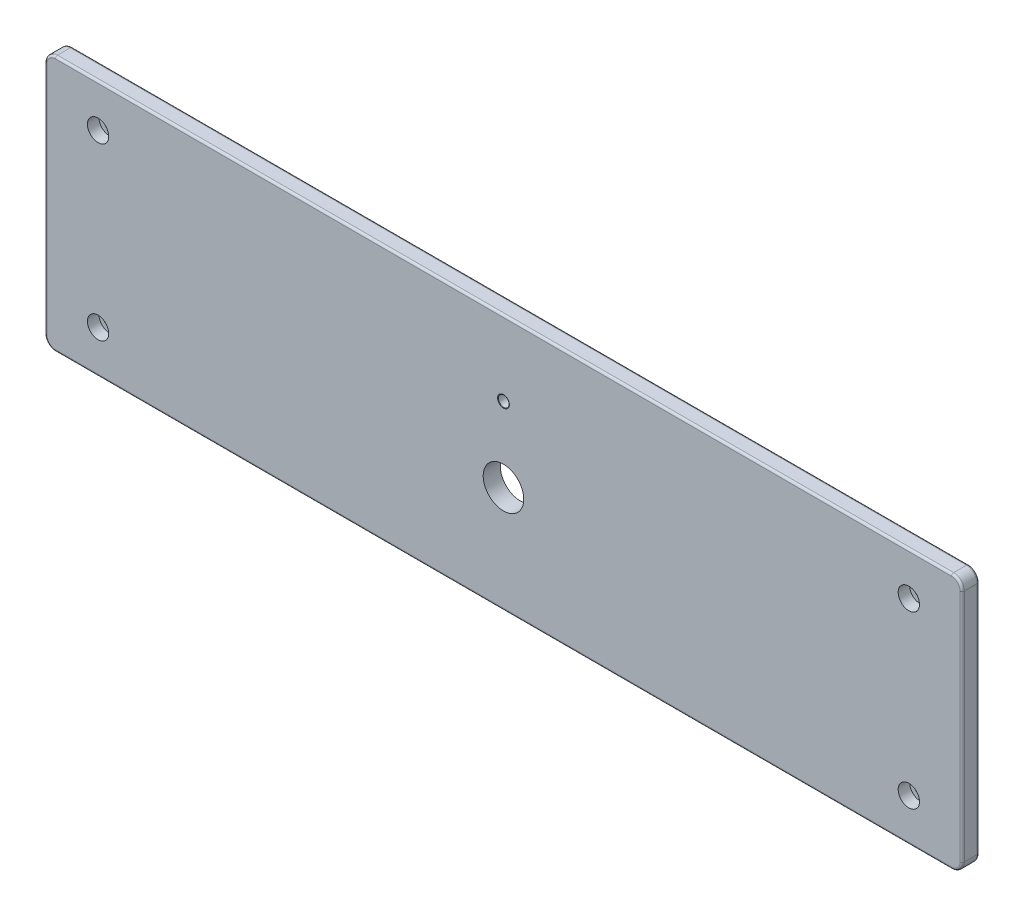
SolidWorks part; units mm, degrees
material "7079 Alloy"
ref_plane "Front Plane" through (0, 0, 0) normal (0, 0, 1) x (1, 0, 0)
ref_plane "Top Plane" through (0, 0, 0) normal (0, 1, 0) x (1, 0, 0)
ref_plane "Right Plane" through (0, 0, 0) normal (1, 0, 0) x (0, 0, -1)
sketch "Sketch1" plane through (0, 0, 0) normal (0, 0, 1) x (1, 0, 0)
  line L1 (0, 0) -> (430, 0)
  line L2 (0, 0) -> (0, 120)
  line L3 (0, 120) -> (430, 120)
  line L4 (430, 0) -> (430, 120)
extrude "Extrude1" add sketch "Sketch1" along normal blind 8
fillet "Fillet1" radius 5 4 edges at (0, 0, 4) (430, 0, 4) (430, 120, 4) (0, 120, 4)
fillet "Fillet2" radius 1 16 edges at (428.5355, 1.4645, 0) (1.4645, 118.5355, 0) (0, 60, 0) (1.4645, 1.4645, 0) (215, 0, 0) (428.5355, 118.5355, 0) (430, 60, 0) (1.4645, 118.5355, 8) (428.5355, 118.5355, 8) (430, 60, 8) (428.5355, 1.4645, 8) (215, 0, 8) (1.4645, 1.4645, 8) (0, 60, 8) (215, 120, 0) (215, 120, 8)
sketch "Sketch2" plane through (0, 0, 8) normal (0, 0, 1) x (1, 0, 0)
  line L0 (25, 20) -> (25, 100) construction
  line L1 (25, 100) -> (405, 100) construction
  line L2 (405, 100) -> (405, 20) construction
  line L3 (405, 20) -> (25, 20) construction
  line L4 (215, 20) -> (215, 50) construction
  line L5 (215, 50) -> (215, 85) construction
  line L6 (215, 85) -> (215, 100) construction
hole_wizard "Ø5.0 (5) Diameter Hole1" positions "3DSketch2" profile "Sketch5" hole size "Ø5.0" standard "DIN" end condition through all
sketch3d "3DSketch2"
  point P0 (215, 85, 8)
sketch "Sketch5" plane through (215, 85, 8) normal (1, 0, 0) x (0, -1, 0)
  line L0 (0, 0) -> (0, 8)
  line L1 (0, 8) -> (2.5, 8)
  line L2 (2.5, 8) -> (2.5, 0)
  line L5 (2.5, 0) -> (0, 0)
  line L11 (0, -6.35) -> (0, 107.95) construction
  dimension "Thru Hole Dia." = 5
  dimension "Thru Hole Depth" = 8
hole_wizard "Ø19.0 (19) Diameter Hole1" positions "3DSketch3" profile "Sketch6" hole size "Ø19.0" standard "DIN" end condition through all
sketch3d "3DSketch3"
  point P0 (215, 50, 8)
sketch "Sketch6" plane through (215, 50, 8) normal (1, 0, 0) x (0, -1, 0)
  line L0 (0, 0) -> (0, 8)
  line L1 (0, 8) -> (9.5, 8)
  line L2 (9.5, 8) -> (9.5, 0)
  line L5 (9.5, 0) -> (0, 0)
  line L11 (0, -6.35) -> (0, 107.95) construction
  dimension "Thru Hole Dia." = 19
  dimension "Thru Hole Depth" = 8
chamfer "Chamfer1" distance 0.25 angle 30 1 edges at (217.5, 85, 8)
hole_wizard "CBORE for M5 Hex Socket Head Cap Screw1" positions "3DSketch4" profile "Sketch9" counterbore size "M5" standard "DIN" end condition through all
sketch3d "3DSketch4"
  point P0 (25, 20, 8)
  point P3 (25, 100, 8)
  point P6 (405, 20, 8)
  point P9 (405, 100, 8)
sketch "Sketch9" plane through (25, 20, 8) normal (1, 0, 0) x (0, -1, 0)
  line L0 (0, 0) -> (0, 8)
  line L1 (0, 8) -> (2.75, 8)
  line L3 (2.75, 8) -> (2.75, 5.4)
  line L4 (2.75, 5.4) -> (5, 5.4)
  line L5 (5, 5.4) -> (5, 0)
  line L7 (5, 0) -> (0, 0)
  line L11 (0, -6.35) -> (0, 107.95) construction
  dimension "Thru Hole Dia." = 5.5
  dimension "Thru Hole Depth" = 8
  dimension "C'Bore Dia." = 10
  dimension "C'Bore Depth" = 5.4
